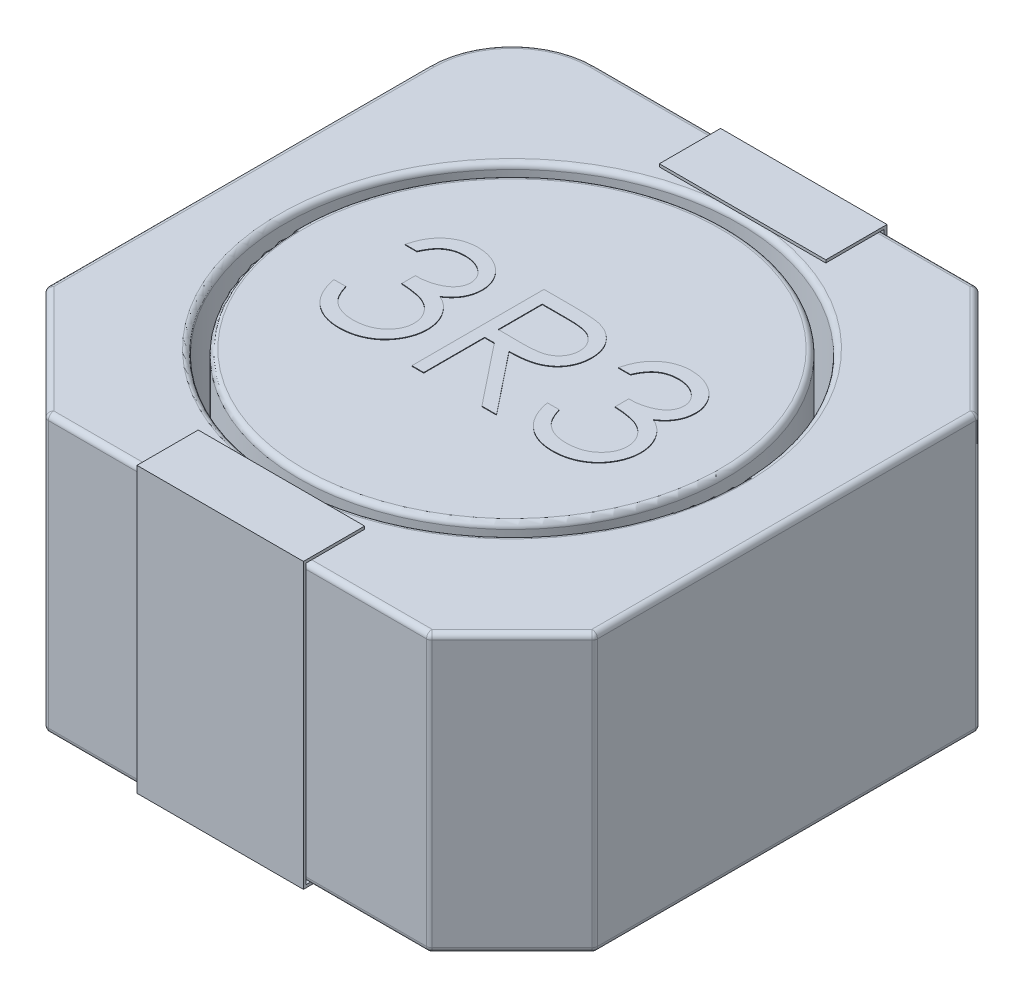
SolidWorks part; units mm, degrees
ref_plane "前视" through (0, 0, 0) normal (0, 0, 1) x (1, 0, 0)
ref_plane "上视" through (0, 0, 0) normal (0, 1, 0) x (1, 0, 0)
ref_plane "右视" through (0, 0, 0) normal (1, 0, 0) x (0, 0, -1)
sketch "草图1" plane through (0, 0, 0) normal (0, 1, 0) x (1, 0, 0)
  line L0 (5.2, -3.7) -> (3.7, -5.2)
  line L1 (-3.7, 5.2) -> (3.2, 5.2)
  line L2 (-5.2, 3.7) -> (-5.2, -3.2)
  line L3 (-3.2, -5.2) -> (3.7, -5.2)
  line L4 (5.2, 3.2) -> (5.2, -3.7)
  line L7 (-5.2, -3.2) -> (-3.2, -5.2)
  line L8 (3.2, 5.2) -> (5.2, 3.2)
  arc A0 (-3.7, 5.2) -> (-5.2, 3.7) centre (-3.7, 3.7) ccw
  point P0 (0, 0)
extrude "凸台-拉伸1" add sketch "草图1" along normal blind 5
sketch "草图2" plane through (0, 5, 0) normal (0, 1, 0) x (1, 0, 0)
  circle A0 centre (0, 0) radius 3.85
  circle A1 centre (0, 0) radius 4.1
extrude "切除-拉伸1" cut sketch "草图2" against normal blind 3.5
sketch "草图3" plane through (0, 0, 0) normal (1, 0, 0) x (0, 0, -1)
  line L0 (-4.1564, 5.01) -> (-5.21, 5.01)
  line L1 (-5.21, 5.01) -> (-5.21, -0.01)
  line L2 (-5.21, -0.01) -> (-4.0282, -0.01)
  line L3 (-4.0282, -0.01) -> (-4.0282, -0.06)
  line L4 (-4.0282, -0.06) -> (-5.26, -0.06)
  line L5 (-5.26, -0.06) -> (-5.26, 5.06)
  line L6 (-5.26, 5.06) -> (-4.1564, 5.06)
  line L7 (-4.1564, 5.06) -> (-4.1564, 5.01)
  line L11 (0, 1.8649) -> (0, 0.8205) construction
  line L12 (4.1564, 5.06) -> (4.1564, 5.01)
  line L13 (5.26, 5.06) -> (4.1564, 5.06)
  line L14 (5.26, -0.06) -> (5.26, 5.06)
  line L15 (4.0282, -0.06) -> (5.26, -0.06)
  line L16 (4.0282, -0.01) -> (4.0282, -0.06)
  line L17 (5.21, -0.01) -> (4.0282, -0.01)
  line L18 (5.21, 5.01) -> (5.21, -0.01)
  line L19 (4.1564, 5.01) -> (5.21, 5.01)
extrude "凸台-拉伸2" add sketch "草图3" along normal mid plane 3 separate body
fillet "圆角1" radius 0.1 9 edges at (-0.25, 5, -5.2) (4.2, 5, -4.2) (5.2, 5, 0.25) (4.45, 5, 4.45) (0.25, 5, 5.2) (-4.2, 5, 4.2) (-5.2, 5, -0.25) (-4.7607, 5, -4.7607) (0, 5, 4.1)
fillet "圆角2" radius 0.1 1 edges at (0, 5, 3.85)
fillet "圆角3" radius 0.1 8 edges at (-5.2, 0, -0.25) (-4.2, 0, 4.2) (0.25, 0, 5.2) (4.45, 0, 4.45) (5.2, 0, 0.25) (4.2, 0, -4.2) (-0.25, 0, -5.2) (-4.7607, 0, -4.7607)
fillet "圆角4" radius 0.1 12 edges at (5.1707, 4.9707, 3.6879) (5.1707, 0.0293, 3.6879) (3.6879, 4.9707, 5.1707) (3.6879, 0.0293, 5.1707) (-3.1879, 4.9707, 5.1707) (-3.1879, 0.0293, 5.1707) (-5.1707, 4.9707, 3.1879) (-5.1707, 0.0293, 3.1879) (5.2, 2.5, 3.7) (3.7, 2.5, 5.2) (-3.2, 2.5, 5.2) (-5.2, 2.5, 3.2)
fillet "圆角5" radius 0.1 6 edges at (3.1879, 4.9707, -5.1707) (3.1879, 0.0293, -5.1707) (5.1707, 4.9707, -3.1879) (5.1707, 0.0293, -3.1879) (3.2, 2.5, -5.2) (5.2, 2.5, -3.2)
sketch "草图4" plane through (0, 5, 0) normal (0, 1, 0) x (1, 0, 0)
  text T0 "3R3" font "Century Gothic" height in points 9
extrude "凸台-拉伸3" add sketch "草图4" along normal blind 0.01
